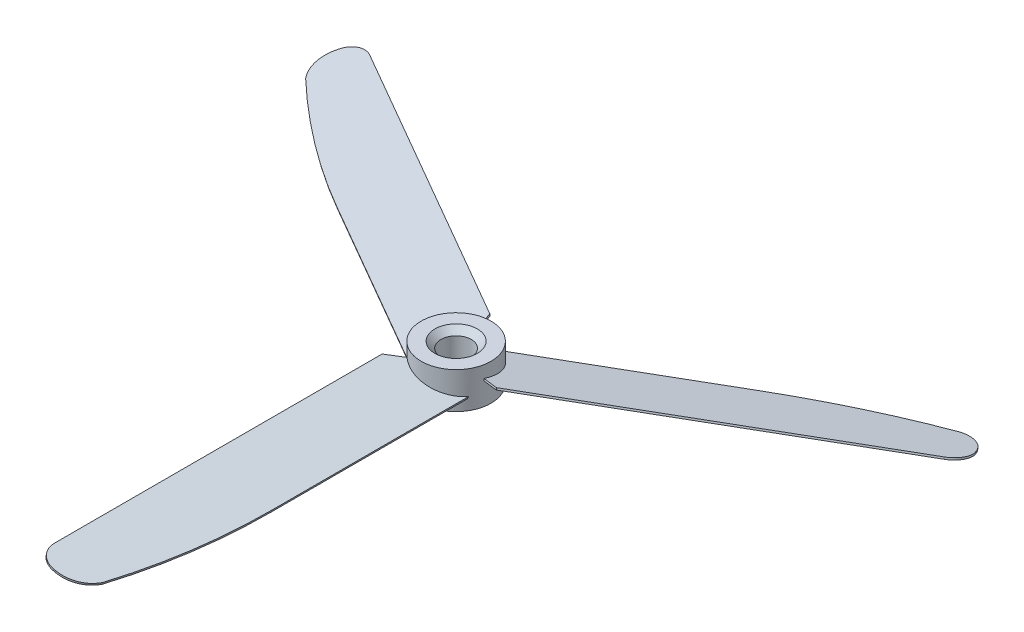
SolidWorks part; units mm, degrees
ref_plane "Front Plane" through (0, 0, 0) normal (0, 0, 1) x (1, 0, 0)
ref_plane "Top Plane" through (0, 0, 0) normal (0, 1, 0) x (1, 0, 0)
ref_plane "Right Plane" through (0, 0, 0) normal (1, 0, 0) x (0, 0, -1)
sketch "Sketch1" plane through (0, 0, 0) normal (0, 1, 0) x (1, 0, 0)
  circle A0 centre (0, 0) radius 5.75
  dimension "D1" = 11.5
extrude "Boss-Extrude1" add sketch "Sketch1" along normal mid plane 6
sketch "Sketch2" plane through (0, 0, 0) normal (0, 0, 1) x (1, 0, 0)
  line L0 (-5.75, 1.3275) -> (5.75, -1.3275) construction
  line L1 (-5.75, 3) -> (-5.75, -3) construction
  line L2 (5.75, -3) -> (5.75, 3) construction
  line L3 (-5.75, -3) -> (5.75, -3) construction
  point P6 (0, 0)
  dimension "D1" = 13
ref_plane "Plane1" through (0, 0, 0) normal (-0.225, -0.9744, 0) x (0.9744, -0.225, 0)
sketch "Sketch3" plane through (0, 0, 0) normal (-0.225, -0.9744, 0) x (0.9744, -0.225, 0)
  line L1 (-3.4012, 3.9449) -> (-5.9675, 6.4172)
  line L2 (-5.9675, 6.4172) -> (-5.9675, 60.5)
  line L3 (-2.9675, 63.5) -> (-2.6441, 63.5)
  line L4 (5.041, 1.3963) -> (5.041, 35.2693)
  arc A1 (2.0247, 60.2895) -> (-2.6441, 63.5) centre (-2.6441, 58.5) ccw
  arc A2 (-5.9675, 60.5) -> (-2.9675, 63.5) centre (-2.9675, 60.5) cw
  arc A3 (5.041, 35.2693) -> (2.0247, 60.2895) centre (-100.239, 35.2693) ccw
  ellipse E0 centre (0.6749, 0) end of major axis (0.6749, 5.75) minor radius 5.6026 construction
  spline S0 degree 2 poles (-3.4012, 3.9449) (1.6507, 7.537) (5.041, 1.3963) knots 0 0 0 1 1 1
  dimension "D2" = 5
  dimension "D3" = 3
  dimension "D1" = 63.5
extrude "Boss-Extrude2" add sketch "Sketch3" along normal mid plane 0.3
pattern_circular "CirPattern1" count 3 over 360 about axis through (0, 0, 0) along (0, 1, 0) of "Boss-Extrude2"
sketch "Sketch4" plane through (0, -3, 0) normal (0, -1, 0) x (1, 0, 0)
  circle A0 centre (0, 0) radius 2.5
  dimension "D1" = 5
extrude "Cut-Extrude1" cut sketch "Sketch4" against normal through all
chamfer "Chamfer1" distance 1 angle 45 2 edges at (0, -3, -2.5) (0, 3, -2.5)
